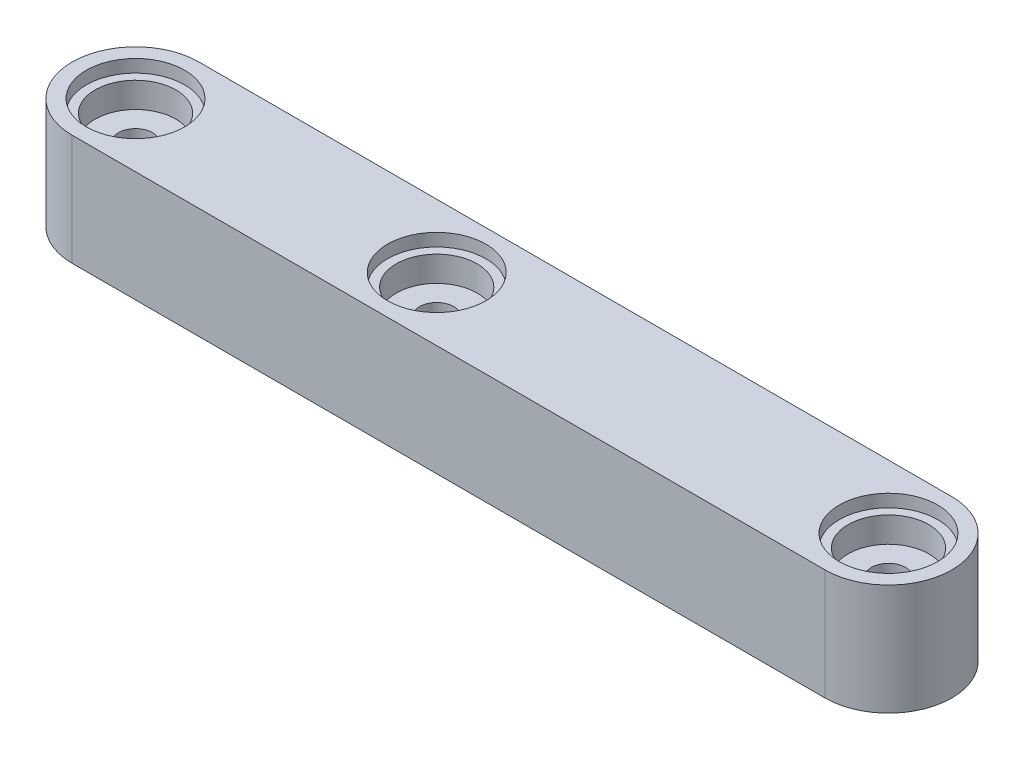
SolidWorks part; units mm, degrees
ref_plane "前视基准面" through (0, 0, 0) normal (0, 0, 1) x (1, 0, 0)
ref_plane "上视基准面" through (0, 0, 0) normal (0, 1, 0) x (1, 0, 0)
ref_plane "右视基准面" through (0, 0, 0) normal (1, 0, 0) x (0, 0, -1)
sketch "草图1" plane through (0, 0, 0) normal (0, 1, 0) x (1, 0, 0)
  line L1 (0, 0) -> (47.5, 0)
  line L3 (0, -8) -> (47.5, -8)
  arc A0 (0, 0) -> (0, -8) centre (0, -4) ccw
  arc A1 (47.5, -8) -> (47.5, 0) centre (47.5, -4) ccw
  circle A2 centre (0, -4) radius 1.075
  circle A3 centre (19, -4) radius 1.075
  circle A4 centre (47.5, -4) radius 1.075
  dimension "D1" = 4
  dimension "D2" = 2.15
  dimension "D3" = 2.15
  dimension "D4" = 2.15
  dimension "D5" = 19
  dimension "D6" = 28.5
extrude "凸台-拉伸1" add sketch "草图1" along normal blind 7
sketch "草图3" plane through (0, 7, 0) normal (0, 1, 0) x (1, 0, 0)
  circle A0 centre (0, -4) radius 2.55
  circle A2 centre (19, -4) radius 2.55
  circle A3 centre (47.5, -4) radius 2.55
  dimension "D1" = 5.1
  dimension "D2" = 5.1
  dimension "D3" = 5.1
extrude "切除-拉伸1" cut sketch "草图3" against normal blind 2.4
sketch "草图4" plane through (0, 7, 0) normal (0, 1, 0) x (1, 0, 0)
  circle A0 centre (0, -4) radius 3.1
  circle A1 centre (19, -4) radius 3.1
  circle A2 centre (47.5, -4) radius 3.1
  dimension "D1" = 6.2
  dimension "D2" = 6.2
  dimension "D3" = 6.2
extrude "切除-拉伸3" cut sketch "草图4" against normal blind 0.8
